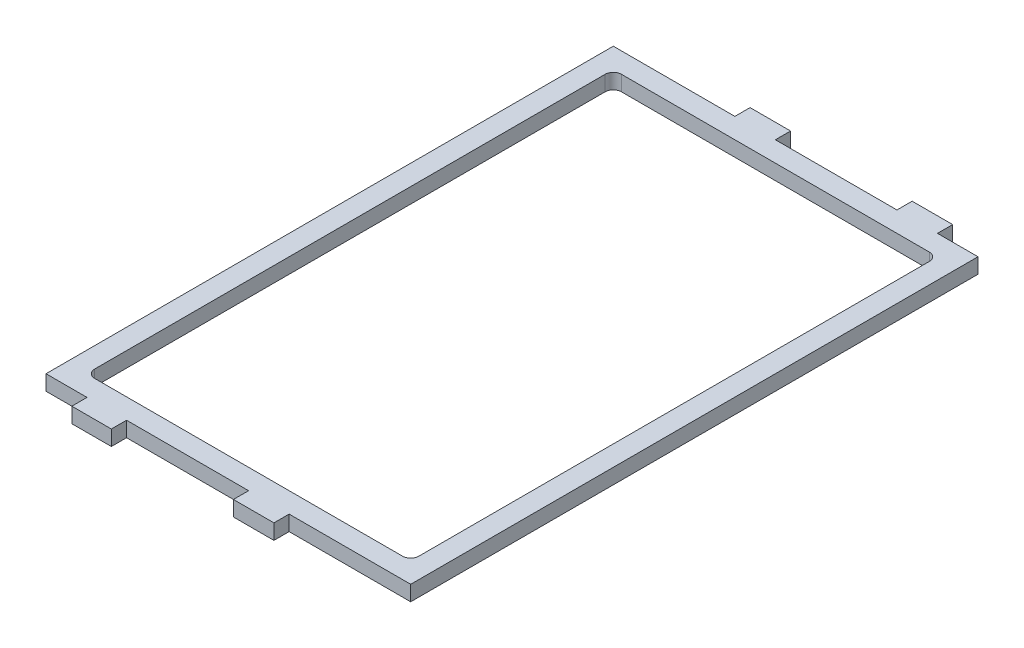
SolidWorks part; units mm, degrees
material "6061-T6 (SS)"
ref_plane "Front Plane" through (0, 0, 0) normal (0, 0, 1) x (1, 0, 0)
ref_plane "Top Plane" through (0, 0, 0) normal (0, 1, 0) x (1, 0, 0)
ref_plane "Right Plane" through (0, 0, 0) normal (1, 0, 0) x (0, 0, -1)
sketch "Sketch1" plane through (0, 0, 0) normal (0, 1, 0) x (1, 0, 0)
  line L0 (50.8, 82.55) -> (-50.8, 82.55)
  line L1 (57.15, 88.9) -> (-57.15, 88.9)
  line L2 (57.15, 88.9) -> (57.15, -88.9)
  line L3 (57.15, -88.9) -> (-57.15, -88.9)
  line L4 (-57.15, 88.9) -> (-57.15, -88.9)
  line L5 (57.15, 88.9) -> (-57.15, -88.9) construction
  line L6 (57.15, -88.9) -> (-57.15, 88.9) construction
  line L7 (-50.8, 82.55) -> (-50.8, -82.55)
  line L8 (50.8, -82.55) -> (-50.8, -82.55)
  line L9 (50.8, 82.55) -> (50.8, -82.55)
  point P0 (0, 0)
  dimension "D1" = 114.3
  dimension "D2" = 177.8
  dimension "D3" = 6.35
extrude "Boss-Extrude1" add sketch "Sketch1" along normal blind 4.7625
sketch "Sketch2" plane through (0, 0, 88.9) normal (0, 0, 1) x (1, 0, 0)
  line L0 (-57.15, 2.3813) -> (57.15, 2.3813) construction
  line L1 (-57.15, 4.7625) -> (-57.15, 0) construction
  line L2 (57.15, 4.7625) -> (57.15, 0) construction
  line L3 (-57.15, 0) -> (57.15, 0) construction
  line L4 (-31.9066, 4.7625) -> (-44.2934, 4.7625)
  line L5 (-31.9066, 4.7625) -> (-31.9066, 0)
  line L6 (-31.9066, 0) -> (-44.2934, 0)
  line L7 (-44.2934, 4.7625) -> (-44.2934, 0)
  line L8 (-31.9066, 4.7625) -> (-44.2934, 0) construction
  line L9 (-31.9066, 0) -> (-44.2934, 4.7625) construction
  line L11 (19.05, 4.7625) -> (6.35, 4.7625)
  line L12 (19.05, 4.7625) -> (19.05, 0)
  line L13 (19.05, 0) -> (6.35, 0)
  line L14 (6.35, 4.7625) -> (6.35, 0)
  line L15 (19.05, 4.7625) -> (6.35, 0) construction
  line L16 (19.05, 0) -> (6.35, 4.7625) construction
  point P6 (-38.1, 2.3813)
  point P13 (12.7, 2.3813)
  dimension "D1" = 19.05
  dimension "D2" = 50.8
  dimension "D3" = 12.7
extrude "Boss-Extrude2" add sketch "Sketch2" along normal blind 4.7625
sketch "Sketch3" plane through (0, 0, -88.9) normal (0, 0, -1) x (-1, 0, 0)
  line L0 (-57.15, 2.3813) -> (57.15, 2.3813) construction
  line L1 (-57.15, 4.7625) -> (-57.15, 0) construction
  line L2 (57.15, 4.7625) -> (57.15, 0) construction
  line L3 (-57.15, 0) -> (57.15, 0) construction
  line L4 (-31.75, 4.7625) -> (-44.45, 4.7625)
  line L5 (-31.75, 4.7625) -> (-31.75, 0)
  line L6 (-31.75, 0) -> (-44.45, 0)
  line L7 (-44.45, 4.7625) -> (-44.45, 0)
  line L8 (-31.75, 4.7625) -> (-44.45, 0) construction
  line L9 (-31.75, 0) -> (-44.45, 4.7625) construction
  line L11 (19.05, 4.7625) -> (6.35, 4.7625)
  line L12 (19.05, 4.7625) -> (19.05, 0)
  line L13 (19.05, 0) -> (6.35, 0)
  line L14 (6.35, 4.7625) -> (6.35, 0)
  line L15 (19.05, 4.7625) -> (6.35, 0) construction
  line L16 (19.05, 0) -> (6.35, 4.7625) construction
  point P6 (-38.1, 2.3812)
  point P13 (12.7, 2.3812)
  dimension "D1" = 12.7
  dimension "D2" = 12.7
  dimension "D3" = 19.05
  dimension "D4" = 50.8
extrude "Boss-Extrude3" add sketch "Sketch3" along normal blind 4.7625
fillet "Fillet1" radius 2.54 4 edges at (50.8, 2.3813, 82.55) (50.8, 2.3813, -82.55) (-50.8, 2.3813, -82.55) (-50.8, 2.3813, 82.55)
